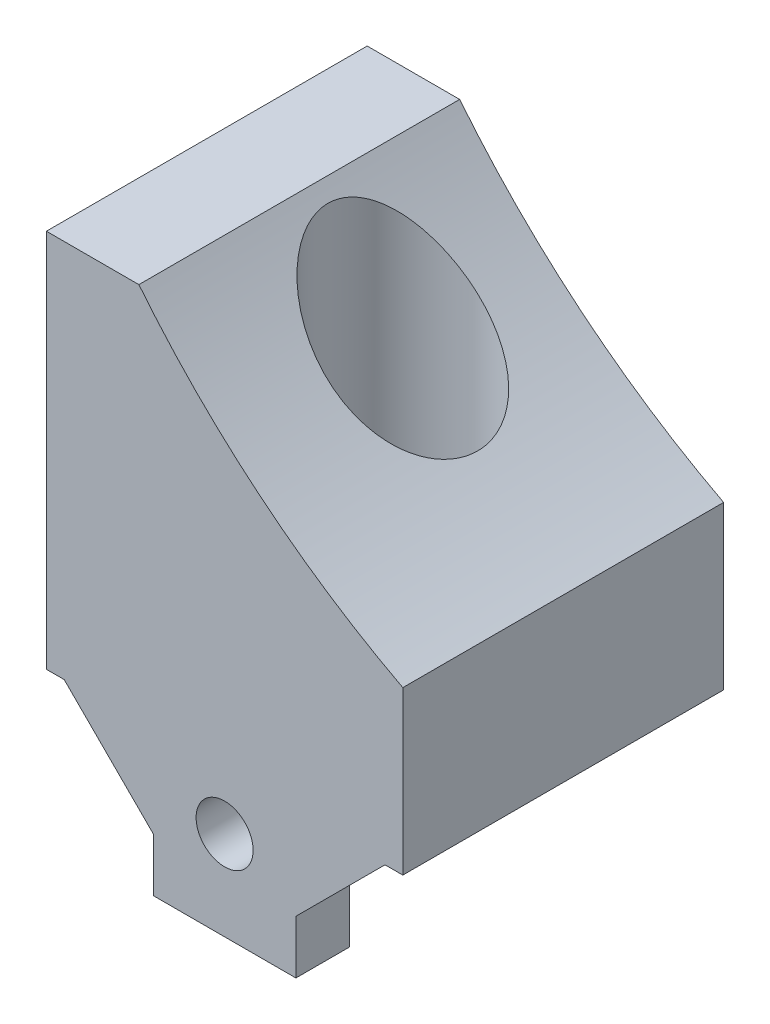
SolidWorks part; units mm, degrees
ref_plane "前视基准面" through (0, 0, 0) normal (0, 0, 1) x (1, 0, 0)
ref_plane "上视基准面" through (0, 0, 0) normal (0, 1, 0) x (1, 0, 0)
ref_plane "右视基准面" through (0, 0, 0) normal (1, 0, 0) x (0, 0, -1)
sketch "草图1" plane through (0, 0, 0) normal (0, 0, 1) x (1, 0, 0)
  line L0 (0, 0) -> (20, 0)
  line L1 (0, 0) -> (0, 21.29)
  line L2 (20, 0) -> (20, 9.1113)
  line L3 (0, 21.29) -> (5.19, 21.29)
  arc A1 (5.19, 21.29) -> (20, 9.1113) centre (41.82, 50.74) ccw
extrude "凸台-拉伸1" add sketch "草图1" along normal blind 18
sketch "草图6" plane through (0, 0, 0) normal (0, -1, 0) x (1, 0, 0)
  circle A0 centre (10, 8) radius 4.2
extrude "切除-拉伸1" cut sketch "草图6" against normal blind 28
sketch "草图7" plane through (0, 0, 0) normal (0, -1, 0) x (1, 0, 0)
  line L0 (10, 18) -> (6, 18)
  line L1 (0, 18) -> (20, 18) construction
  line L2 (10, 18) -> (14, 18)
  line L3 (14, 18) -> (14, 15)
  line L4 (14, 15) -> (6, 15)
  line L5 (6, 15) -> (6, 18)
extrude "凸台-拉伸2" add sketch "草图7" along normal blind 8
chamfer "倒角1" distance 5 angle 45 1 edges
chamfer "倒角2" distance 5 angle 45 1 edges
sketch "草图8" plane through (0, 0, 15) normal (0, 0, -1) x (-1, 0, 0)
  circle A0 centre (-10, -3) radius 1.6
extrude "切除-拉伸2" cut sketch "草图8" against normal blind 8
